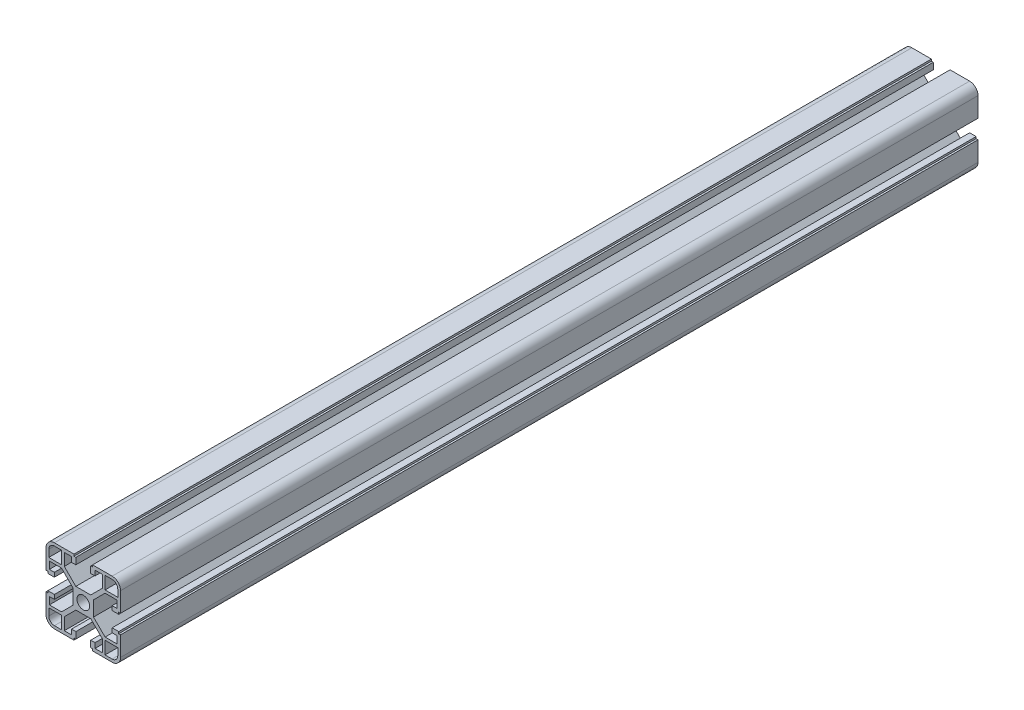
SolidWorks part; units mm, degrees
material "6061-T6 (SS)"
ref_plane "Front Plane" through (0, 0, 0) normal (0, 0, 1) x (1, 0, 0)
ref_plane "Top Plane" through (0, 0, 0) normal (0, 1, 0) x (1, 0, 0)
ref_plane "Right Plane" through (0, 0, 0) normal (1, 0, 0) x (0, 0, -1)
sketch "Sketch1" plane through (0, 0, 0) normal (0, 0, 1) x (1, 0, 0)
  line L0 (3.4, 0) -> (5.5, 0)
  line L1 (10.19, 11.69) -> (4, 5.5)
  line L2 (11.69, 10.19) -> (5.5, 4)
  line L3 (18.2, 10.19) -> (11.69, 10.19)
  line L4 (18.2, 10.19) -> (18.2, 6.3)
  line L5 (18.2, 6.3) -> (15.5, 6.3)
  line L6 (15.5, 6.3) -> (15.5, 4)
  line L7 (15.5, 4) -> (19, 4)
  line L8 (19, 4) -> (19, 5)
  line L9 (19, 5) -> (20, 5)
  line L10 (20, 5) -> (20, 15.5)
  line L11 (15.5, 20) -> (5, 20)
  line L12 (18.5, 11.69) -> (18.5, 15.5)
  line L13 (15.5, 18.5) -> (11.69, 18.5)
  line L14 (11.69, 11.69) -> (11.69, 18.5)
  line L15 (0, 3.4) -> (0, 5.5)
  line L16 (4, 5.5) -> (0, 5.5)
  line L17 (5, 20) -> (5, 19)
  line L18 (5.5, 0) -> (5.5, 4)
  line L19 (5, 19) -> (4, 19)
  line L20 (4, 19) -> (4, 15.5)
  line L21 (4, 15.5) -> (6.3, 15.5)
  line L22 (10.19, 11.69) -> (10.19, 18.2)
  line L23 (11.69, 11.69) -> (18.5, 11.69)
  line L24 (6.3, 18.2) -> (6.3, 15.5)
  line L25 (10.19, 18.2) -> (6.3, 18.2)
  arc A0 (20, 15.5) -> (15.5, 20) centre (15.5, 15.5) ccw
  arc A1 (18.5, 15.5) -> (15.5, 18.5) centre (15.5, 15.5) ccw
  arc A2 (3.4, 0) -> (0, 3.4) centre (0, 0) ccw
  point P4 (0, 4.45)
  dimension "D3" = 4.5
  dimension "D18" = 1.5
  dimension "D9" = 3.4
  dimension "D20" = 1.8
  dimension "D25" = 3
  dimension "D1" = 5.5
  dimension "D2" = 1.5
  dimension "D4" = 14.5
  dimension "D5" = 1.5
  dimension "D6" = 2.1
  dimension "D7" = 2.3
  dimension "D8" = 1.8
  dimension "D10" = 6.81
  dimension "D11" = 2.1
  dimension "D12" = 1
  dimension "D13" = 4.5
  dimension "D14" = 45
  dimension "D15" = 14.5
  dimension "D16" = 1
  dimension "D17" = 1.5
  dimension "D19" = 6.81
  dimension "D21" = 4.5
  dimension "D22" = 2.3
  dimension "D23" = 1
  dimension "D24" = 1
  dimension "D26" = 8.754
  dimension "D27" = 8.754
  dimension "D28" = 4
  dimension "D29" = 4
extrude "Boss-Extrude1" add sketch "Sketch1" along normal blind 460
mirror "Mirror1" about plane through (0, 0, 0) normal (0, 1, 0) of "Boss-Extrude1"
mirror "Mirror2" about plane through (0, 0, 0) normal (1, 0, 0) of "Boss-Extrude1"
mirror "Mirror3" about plane through (0, 0, 0) normal (0, 1, 0) of "Mirror2"
